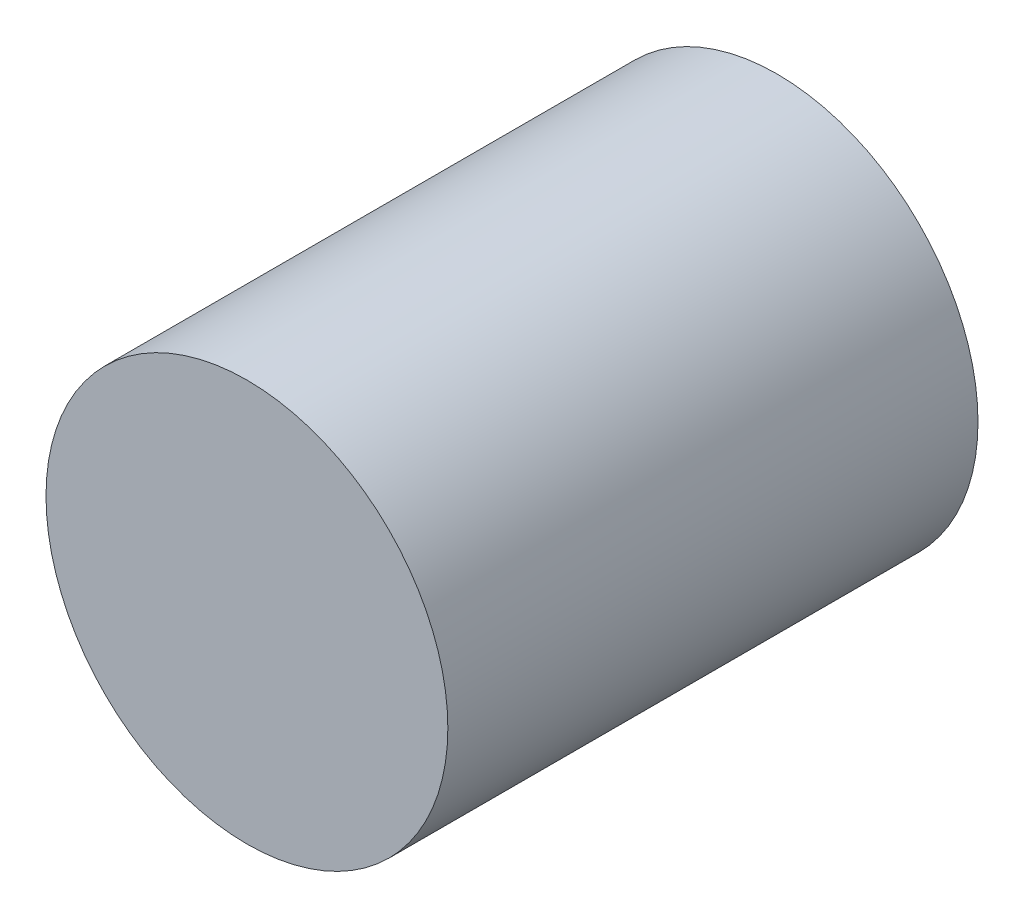
SolidWorks part; units mm, degrees
ref_plane "前视基准面" through (0, 0, 0) normal (0, 0, 1) x (1, 0, 0)
ref_plane "上视基准面" through (0, 0, 0) normal (0, 1, 0) x (1, 0, 0)
ref_plane "右视基准面" through (0, 0, 0) normal (1, 0, 0) x (0, 0, -1)
sketch "草图2" plane through (0, 0, 0) normal (0, 0, 1) x (1, 0, 0)
  line L0 (0, 0) -> (20, 0)
  line L1 (10, 0) -> (10, 20)
  line L2 (-15, 10) -> (0, 10)
  line L3 (-10, 10) -> (-10, -5)
  line L4 (0, 15) -> (0, 0)
  line L5 (-47.3169, -11.7356) -> (-36.8507, -17.2872)
  line L6 (-29.0346, -17.0155) -> (-34.5862, -27.4817)
  line L7 (-25.9968, -11.2885) -> (-17.986, 3.8139)
  line L8 (20, -25.1404) -> (11.2943, -42.0544)
  line L9 (-60.121, 21.9864) -> (-60.121, -2.1935) construction
  line L10 (-92.1575, -19.996) -> (-54.523, -19.996)
  line L11 (-95.9461, -26.0261) -> (-95.9461, -46.0219)
  line L12 (-92.1575, -52.0519) -> (-54.523, -52.0519)
  line L13 (-50.7343, -26.0261) -> (-50.7343, -46.0219)
  line L14 (11.2943, -42.0544) -> (27.6404, -53.0688)
  line L15 (-24.1894, -76.578) -> (-64.0208, -104.1612)
  line L16 (-64.0208, -104.1612) -> (-61.7567, -117.8994)
  line L17 (-61.7567, -117.8994) -> (-8.1539, -117.8994)
  circle A0 centre (-73.3978, 9.6204) radius 13.2767
  circle A1 centre (-46.8443, 9.6204) radius 13.2767
  arc A2 (-92.1575, -19.996) -> (-95.9461, -26.0261) centre (-73.3402, -36.024) ccw
  arc A3 (-95.9461, -46.0219) -> (-92.1575, -52.0519) centre (-73.3402, -36.024) ccw
  arc A4 (-54.523, -52.0519) -> (-50.7343, -46.0219) centre (-73.3402, -36.024) ccw
  arc A5 (-50.7343, -26.0261) -> (-54.523, -19.996) centre (-73.3402, -36.024) ccw
  circle A6 centre (99.1499, -15.0873) radius 15.1605
  dimension "D1" = 10
  dimension "D2" = 15
  dimension "D3" = 5
  dimension "D4" = 20
  dimension "D5" = 10
  dimension "D6" = 48.4497
  dimension "D7" = 39.8314
  dimension "D8" = 27.5832
  dimension "D9" = 34.703
  dimension "D10" = 13.9235
  dimension "D11" = 53.6028
extrude "凸台-拉伸2" add sketch "草图2" against normal blind 40 contours A6
sketch "草图4" plane through (0, 0, -40) normal (0, 0, -1) x (-1, 0, 0)
  line L1 (-106.6499, -7.5873) -> (-91.6499, -7.5873)
  line L2 (-106.6499, -7.5873) -> (-106.6499, -22.5873)
  line L3 (-106.6499, -22.5873) -> (-91.6499, -22.5873)
  line L4 (-91.6499, -7.5873) -> (-91.6499, -22.5873)
  line L5 (-106.6499, -7.5873) -> (-91.6499, -22.5873) construction
  line L6 (-106.6499, -22.5873) -> (-91.6499, -7.5873) construction
  circle A0 centre (-99.1499, -15.0873) radius 15.1605 construction
  circle A1 centre (-99.1499, -15.0873) radius 15.1605
  dimension "D1" = 15
  dimension "D2" = 15
